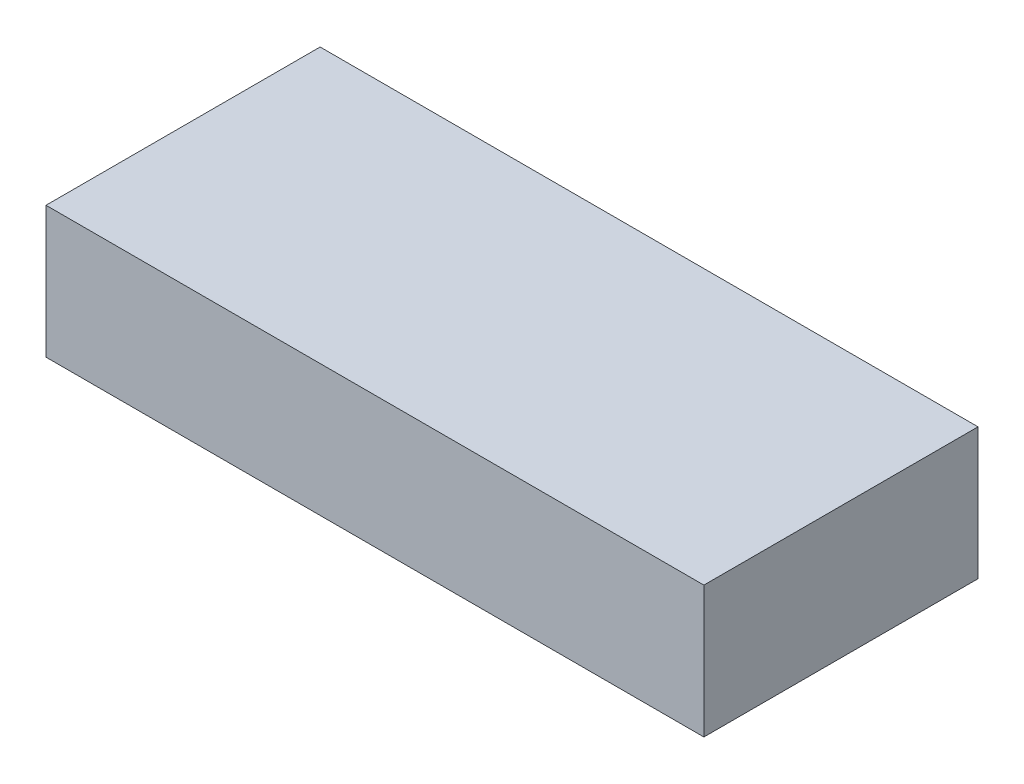
SolidWorks part; units mm, degrees
material "Воздух"
ref_plane "Спереди" through (0, 0, 0) normal (0, 0, 1) x (1, 0, 0)
ref_plane "Сверху" through (0, 0, 0) normal (0, 1, 0) x (1, 0, 0)
ref_plane "Справа" through (0, 0, 0) normal (1, 0, 0) x (0, 0, -1)
sketch "Эскиз1" plane through (0, 0, 0) normal (0, 0, 1) x (1, 0, 0)
  line L1 (-240, 48) -> (240, 48)
  line L2 (-240, 48) -> (-240, -48)
  line L3 (-240, -48) -> (240, -48)
  line L4 (240, 48) -> (240, -48)
  line L5 (-240, 48) -> (240, -48) construction
  line L6 (-240, -48) -> (240, 48) construction
  point P0 (0, 0)
  dimension "D1" = 480
  dimension "D2" = 96
extrude "Бобышка-Вытянуть1" add sketch "Эскиз1" along normal blind 200
